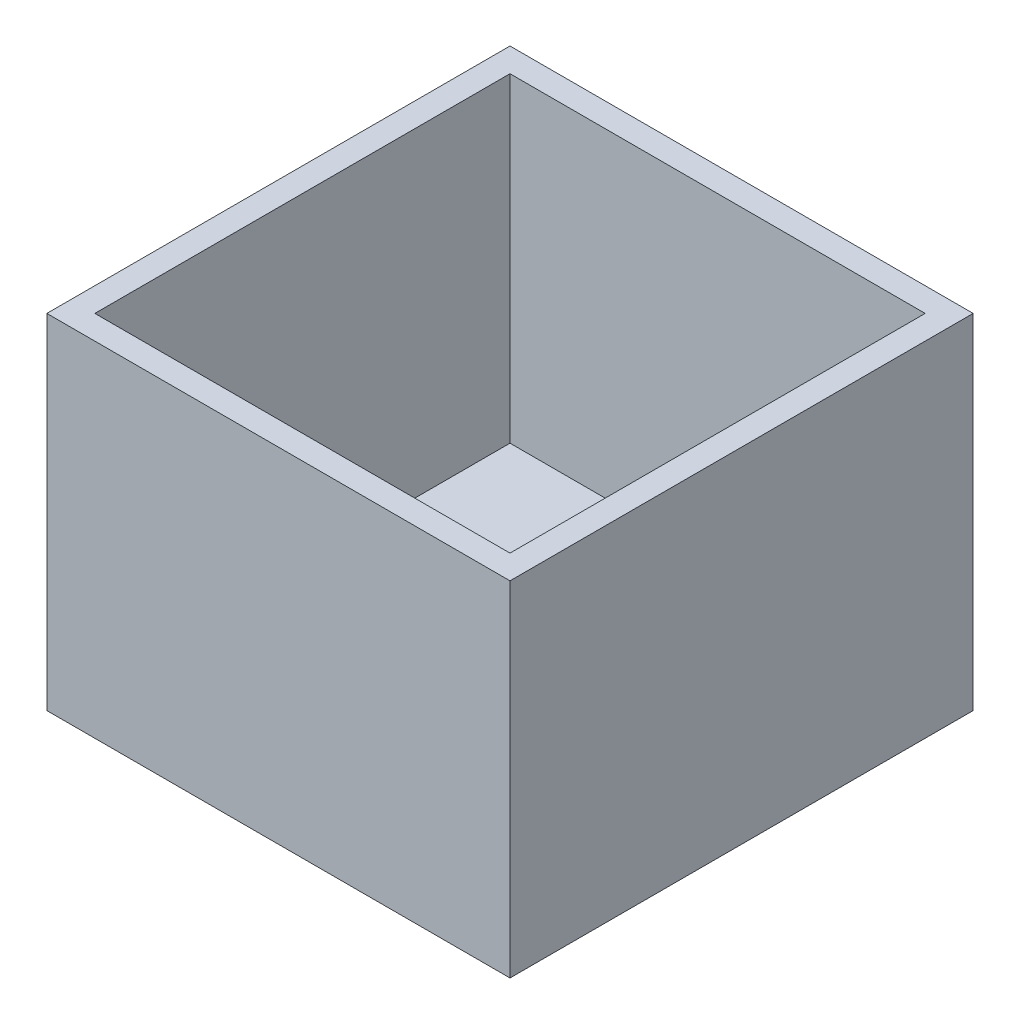
SolidWorks part; units mm, degrees
ref_plane "前视基准面" through (0, 0, 0) normal (0, 0, 1) x (1, 0, 0)
ref_plane "上视基准面" through (0, 0, 0) normal (0, 1, 0) x (1, 0, 0)
ref_plane "右视基准面" through (0, 0, 0) normal (1, 0, 0) x (0, 0, -1)
sketch "草图1" plane through (0, 0, 0) normal (0, 1, 0) x (1, 0, 0)
  line L0 (-3, -3) -> (-3, 54.9)
  line L5 (-3, 54.9) -> (54.9, 54.9)
  line L6 (54.9, -3) -> (54.9, 54.9)
  line L7 (-3, -3) -> (54.9, -3)
  dimension "D1" = 57.9
extrude "凸台-拉伸1" add sketch "草图1" along normal blind 3
sketch "草图2" plane through (0, 3, 0) normal (0, 1, 0) x (1, 0, 0)
  line L14 (51.9, 0) -> (51.9, 51.9)
  line L15 (0, 0) -> (51.9, 0)
  line L16 (0, 51.9) -> (0, 0)
  line L17 (51.9, 51.9) -> (0, 51.9)
  line L18 (51.9, 0) -> (51.9, 51.9)
  line L19 (0, 0) -> (51.9, 0)
  line L20 (0, 51.9) -> (0, 0)
  line L21 (51.9, 51.9) -> (0, 51.9)
  line L26 (-3, -3) -> (54.9, -3)
  line L27 (54.9, -3) -> (54.9, 54.9)
  line L28 (54.9, 54.9) -> (-3, 54.9)
  line L29 (-3, 54.9) -> (-3, -3)
  line L30 (-3, -3) -> (54.9, -3)
  line L31 (54.9, -3) -> (54.9, 54.9)
  line L32 (54.9, 54.9) -> (-3, 54.9)
  line L33 (-3, 54.9) -> (-3, -3)
  dimension "D1" = 3
  dimension "D2" = 0
extrude "凸台-拉伸2" add sketch "草图2" along normal blind 40
